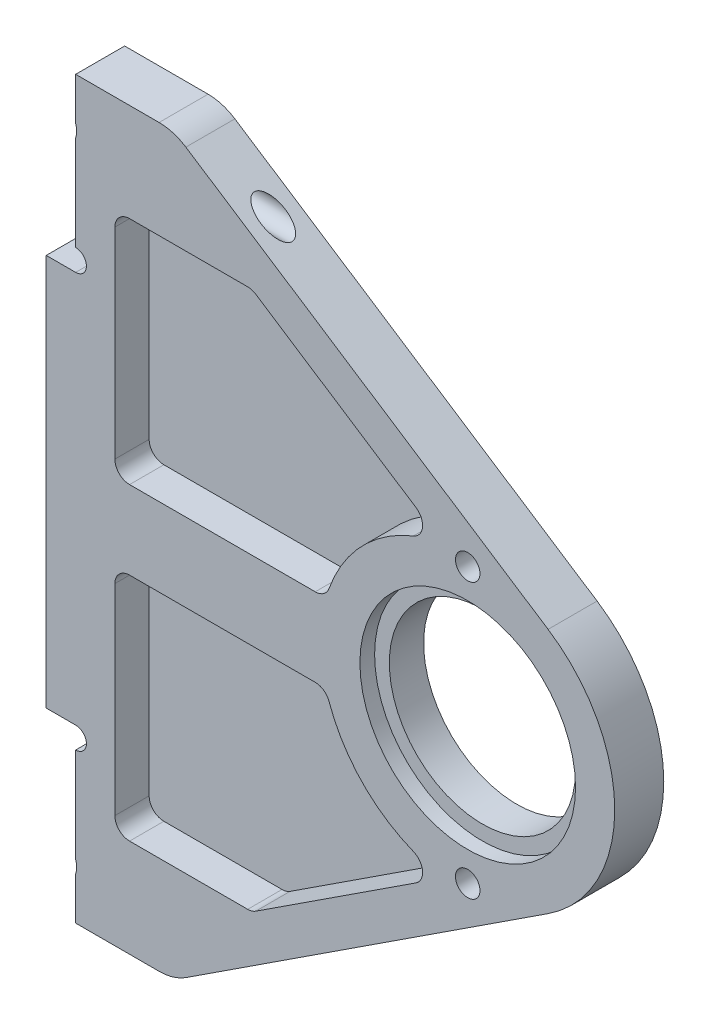
SolidWorks part; units mm, degrees
other "ﾏｰｸｱｯﾌﾟ1"
sketch "ｽｹｯﾁ9" plane through (-43, -37.5, 5) normal (-0.4071, -0.0601, 0.9114) x (-0.9124, -0.0192, -0.4088)
material "3.1325 (EN-AW 2017A)"
ref_plane "正面" through (0, 0, 0) normal (0, 0, 1) x (1, 0, 0)
ref_plane "平面" through (0, 0, 0) normal (0, 1, 0) x (1, 0, 0)
ref_plane "右側面" through (0, 0, 0) normal (1, 0, 0) x (0, 0, -1)
sketch "ｽｹｯﾁ2" plane through (0, 0, 0) normal (0, 0, 1) x (1, 0, 0)
  line L1 (0, -14) -> (0, 14) construction
  line L2 (0, 0) -> (-30, 0) construction
  line L4 (-40, 20) -> (-43, 20)
  line L5 (-40, 37.5) -> (-40, -37.5)
  line L6 (-40, -37.5) -> (-30, -37.5)
  line L7 (-40, 37.5) -> (-30, 37.5)
  line L8 (-30, 37.5) -> (-30, -37.5) construction
  line L9 (-30, 37.5) -> (8.2002, 12.5601)
  line L10 (-30, -37.5) -> (8.2002, -12.5601)
  line L11 (-40, 0) -> (-30, 0) construction
  line L12 (0, -15) -> (-40, -15) construction
  line L13 (-40, -15) -> (-40, -37.5) construction
  line L14 (0, -30) -> (-40, -30) construction
  line L15 (-40, -37.5) -> (-40, -30) construction
  line L16 (-40, -57.5) -> (-30, -57.5) construction
  line L17 (-30, -57.5) -> (-30, -37.5) construction
  line L18 (-40, 20) -> (-40, -20)
  line L19 (-40, -20) -> (-43, -20)
  line L20 (-43, 20) -> (-43, -20)
  circle A0 centre (0, 0) radius 9.5
  circle A1 centre (0, 14) radius 1.25
  circle A3 centre (0, -14) radius 1.25
  arc A8 (8.2002, -12.5601) -> (8.2002, 12.5601) centre (0, 0) ccw
  circle A9 centre (0, 0) radius 30 construction
  point P6 (0, 0)
  point P9 (0, 0)
  point P14 (-30, 0)
  point P29 (-35, 0)
  point P37 (-40, 0)
  dimension "D1" = 19
  dimension "D2" = 2.5
  dimension "D3" = 75
  dimension "D4" = 40
  dimension "D5" = 3
  dimension "D8" = 15
  dimension "D9" = 10
  dimension "D12" = 60
  dimension "D13" = 30
  dimension "D6" = 2.5
  dimension "D7" = 28
  dimension "D15" = 20
  dimension "D16" = 27.5
extrude "ﾎﾞｽ - 押し出し1" add sketch "ｽｹｯﾁ2" along normal blind 5
fillet "ﾌｨﾚｯﾄ3" radius 5 2 edges at (-30, 37.5, 2.5) (-30, -37.5, 2.5)
sketch "ｽｹｯﾁ3" plane through (-40, 0, 0) normal (-1, 0, 0) x (0, 0, 1)
  line L0 (5, -37.5) -> (0, -37.5) construction
  line L1 (5, -20) -> (5, -37.5) construction
  line L2 (5, 37.5) -> (5, 20) construction
  line L3 (5, 37.5) -> (0, 37.5) construction
  circle A0 centre (2.5, -32.5) radius 1.25
  circle A1 centre (2.5, 32.5) radius 1.25
  dimension "D1" = 2.5
  dimension "D2" = 2.5
  dimension "D3" = 5
  dimension "D4" = 2.5
  dimension "D5" = 2.5
  dimension "D6" = 5
extrude "ｶｯﾄ - 押し出し1" cut sketch "ｽｹｯﾁ3" against normal through all
sketch "ｽｹｯﾁ4" plane through (0, 0, 0) normal (0, 0, -1) x (-1, 0, 0)
  line L0 (40, 20) -> (43, 20) construction
  line L1 (40, -20) -> (43, -20) construction
  circle A0 centre (40, 21.1) radius 1.1
  circle A1 centre (40, -21.1) radius 1.1
  dimension "D1" = 2.2
  dimension "D2" = 2.2
extrude "ｶｯﾄ - 押し出し2" cut sketch "ｽｹｯﾁ4" against normal blind 10 contours A1 | A0
sketch "ｽｹｯﾁ5" plane through (0, 0, 0) normal (0, 0, -1) x (-1, 0, 0)
  line L0 (40, 37.5) -> (40, 22.2) construction
  line L1 (40, 37.5) -> (31.4877, 37.5) construction
  line L2 (40, -37.5) -> (31.4877, -37.5) construction
  circle A0 centre (42, 32.5) radius 2.1
  circle A1 centre (42, -32.5) radius 2.1
  dimension "D1" = 4.2
  dimension "D2" = 2
  dimension "D3" = 5
  dimension "D5" = 5
  dimension "D4" = 2
extrude "ｶｯﾄ - 押し出し3" cut sketch "ｽｹｯﾁ5" against normal blind 10
sketch "ｽｹｯﾁ7" plane through (0, 0, 5) normal (0, 0, 1) x (1, 0, 0)
  circle A0 centre (0, 0) radius 11
  dimension "D1" = 22
extrude "ｶｯﾄ - 押し出し5" cut sketch "ｽｹｯﾁ7" against normal blind 1.5
sketch "ｽｹｯﾁ8" plane through (0, 0, 5) normal (0, 0, 1) x (1, 0, 0)
  line L0 (-43, 20) -> (-43, -20) construction
  line L1 (-36, -4) -> (-36, -27.5)
  line L2 (-30.941, 33.3373) -> (6.0135, 9.2108)
  line L3 (-22, 27.5) -> (-2.5258, 14.7858)
  line L4 (-36, 4) -> (-36, -4) construction
  line L5 (-30.941, -33.3373) -> (6.0135, -9.2108)
  line L6 (-22, -27.5) -> (-2.5258, -14.7858)
  line L8 (-40, -27.5) -> (-31.4877, -27.5)
  line L9 (-36, -27.5) -> (-22, -27.5)
  line L10 (-36, 27.5) -> (-36, 4)
  line L11 (-40, 27.5) -> (-31.4877, 27.5)
  line L12 (-36, 27.5) -> (-22, 27.5)
  line L13 (-40, 31.8597) -> (-40, 22.2) construction
  line L14 (-36, 4) -> (-14.4568, 4)
  line L15 (-36, -4) -> (-14.4568, -4)
  arc A0 (-2.5258, 14.7858) -> (-14.4568, 4) centre (0, 0) ccw
  arc A1 (8.2002, -12.5601) -> (8.2002, 12.5601) centre (0, 0) ccw construction
  arc A2 (-2.5258, -14.7858) -> (-2.5258, 14.7858) centre (0, 0) ccw construction
  arc A3 (-14.4568, -4) -> (-2.5258, -14.7858) centre (0, 0) ccw
  arc A4 (-14.4568, 4) -> (-14.4568, -4) centre (0, 0) ccw construction
  point P27 (-43, 0)
  dimension "D5" = 4
  dimension "D6" = 8
  dimension "D7" = 4
  dimension "D1" = 4
  dimension "D2" = 4
  dimension "D3" = 10
  dimension "D4" = 10
extrude "ｶｯﾄ - 押し出し6" cut sketch "ｽｹｯﾁ8" against normal blind 3.5
fillet "ﾌｨﾚｯﾄ5" radius 1.5 10 edges at (-36, -27.5, 3.25) (-22, -27.5, 3.25) (-2.5258, -14.7858, 3.25) (-14.4568, -4, 3.25) (-36, -4, 3.25) (-36, 4, 3.25) (-14.4568, 4, 3.25) (-2.5258, 14.7858, 3.25) (-22, 27.5, 3.25) (-36, 27.5, 3.25)
